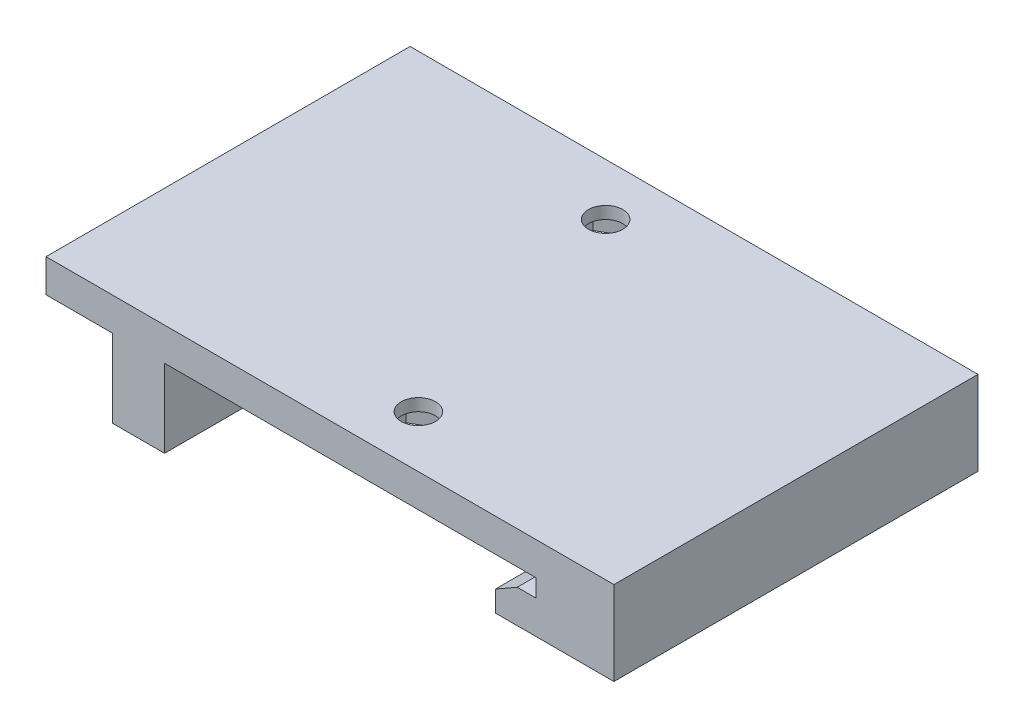
SolidWorks part; units mm, degrees
ref_plane "Front Plane" through (0, 0, 0) normal (0, 0, 1) x (1, 0, 0)
ref_plane "Top Plane" through (0, 0, 0) normal (0, 1, 0) x (1, 0, 0)
ref_plane "Right Plane" through (0, 0, 0) normal (1, 0, 0) x (0, 0, -1)
sketch "Sketch1" plane through (0, 0, 0) normal (0, 0, 1) x (1, 0, 0)
  line L0 (0, 0) -> (19.8, 0)
  line L1 (19.8, 0) -> (19.8, -1.7)
  line L2 (19.8, -1.7) -> (18, -1.7)
  line L3 (18, -1.7) -> (15.9, -2.9)
  line L4 (15.9, -2.9) -> (15.9, -4.9)
  line L5 (15.9, -4.9) -> (27.3, -4.9)
  line L8 (27.3, 3.175) -> (-27.3, 3.175)
  line L10 (-20.9, -7.5) -> (-15.9, -7.5)
  line L11 (-15.9, -7.5) -> (-15.9, 0)
  line L12 (-15.9, 0) -> (0, 0)
  line L16 (0, 0) -> (0, 6.355) construction
  line L20 (27.3, 3.175) -> (27.3, -4.9)
  line L21 (-27.3, 3.175) -> (-27.3, 0)
  line L22 (-27.3, 0) -> (-20.9, 0)
  line L23 (-20.9, 0) -> (-20.9, -7.5)
  dimension "D2" = 1.8
  dimension "D3" = 3.9
  dimension "D4" = 3.2
  dimension "D5" = 1.7
  dimension "D6" = 1.2
  dimension "D7" = 5
  dimension "D8" = 7.5
  dimension "D9" = 3.175
  dimension "D10" = 15.9
  dimension "D11" = 54.6
  dimension "D14" = 15.9
extrude "Boss-Extrude1" add sketch "Sketch1" along normal blind 35
sketch "Sketch2" plane through (-20.9, 0, 0) normal (-1, 0, 0) x (0, 0, 1)
  line L0 (17.5, 0) -> (17.5, -7.5) construction
  line L1 (35, 0) -> (0, 0) construction
  line L2 (35, -7.5) -> (0, -7.5) construction
  line L3 (0, 0) -> (17.5, 0) construction
  line L4 (8.75, 0) -> (8.75, -7.5) construction
  line L5 (17.5, 0) -> (35, 0) construction
  line L6 (26.25, 0) -> (26.25, -7.5) construction
  circle A0 centre (8.75, -3.75) radius 1.275
  circle A1 centre (26.25, -3.75) radius 1.275
  point P10 (17.5, -3.75)
  dimension "D1" = 2.55
extrude "Cut-Extrude1" cut sketch "Sketch2" against normal up to surface (5 mm away) up to face at (-15.9, -3.75, 17.5)
sketch "Sketch5" plane through (0, 0, 0) normal (0, -1, 0) x (1, 0, 0)
  line L0 (-15.9, 35) -> (19.8, 35) construction
  line L1 (6.35, 28.3546) -> (6.35, 31.6454)
  line L2 (6.35, 31.6454) -> (3.5, 33.2909)
  line L3 (3.5, 33.2909) -> (0.65, 31.6454)
  line L4 (0.65, 31.6454) -> (0.65, 28.3546)
  line L5 (0.65, 28.3546) -> (3.5, 26.7091)
  line L6 (3.5, 26.7091) -> (6.35, 28.3546)
  line L7 (-0.65, 6.6454) -> (-3.5, 8.2909)
  line L8 (-3.5, 8.2909) -> (-6.35, 6.6454)
  line L9 (-6.35, 6.6454) -> (-6.35, 3.3546)
  line L10 (-6.35, 3.3546) -> (-3.5, 1.7091)
  line L11 (-3.5, 1.7091) -> (-0.65, 3.3546)
  line L12 (-0.65, 3.3546) -> (-0.65, 6.6454)
  line L13 (-15.9, 0) -> (19.8, 0) construction
  circle A0 centre (3.5, 30) radius 2.85 construction
  circle A1 centre (-3.5, 5) radius 2.85 construction
  circle A2 centre (3.5, 30) radius 1.65
  circle A3 centre (-3.5, 5) radius 1.65
  dimension "D4" = 3.3
  dimension "D1" = 5.7
  dimension "D2" = 5
  dimension "D3" = 5
  dimension "D5" = 7
  dimension "D6" = 3.5
extrude "Cut-Extrude2" cut sketch "Sketch5" against normal blind 2
sketch "Sketch6" plane through (0, 0, 0) normal (0, -1, 0) x (1, 0, 0)
  circle A0 centre (3.5, 30) radius 1.65 construction
  circle A1 centre (3.5, 30) radius 1.65
  circle A3 centre (-3.5, 5) radius 1.65
  circle A4 centre (-3.5, 5) radius 1.65
  dimension "D1" = 0
extrude "Cut-Extrude3" cut sketch "Sketch6" against normal through all
